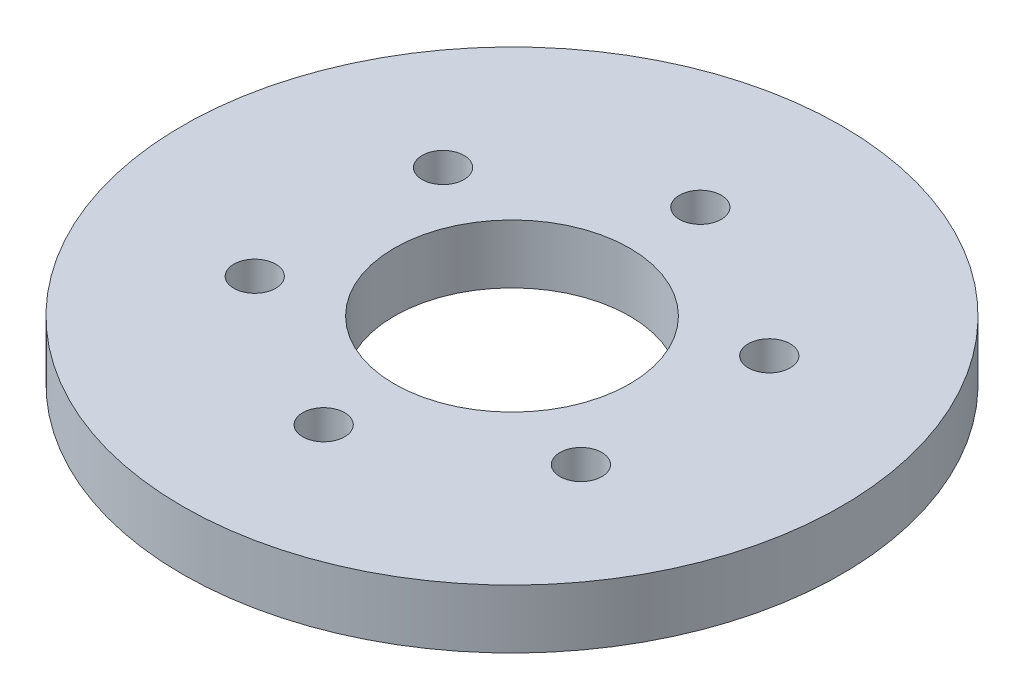
SolidWorks part; units mm, degrees
ref_plane "Front Plane" through (0, 0, 0) normal (0, 0, 1) x (1, 0, 0)
ref_plane "Top Plane" through (0, 0, 0) normal (0, 1, 0) x (1, 0, 0)
ref_plane "Right Plane" through (0, 0, 0) normal (1, 0, 0) x (0, 0, -1)
sketch "Sketch1" plane through (0, 0, 0) normal (0, 1, 0) x (1, 0, 0)
  line L0 (0, 10.16) -> (0, 0) construction
  circle A0 centre (0, 0) radius 6.35
  circle A1 centre (0, 0) radius 17.78
  point P4 (0, 10.16)
  point P6 (-8.7988, 5.08)
  point P7 (-29.4057, -6.7467)
  point P8 (0, 0)
  point P9 (-8.7988, -5.08)
  point P10 (0, -10.16)
  point P11 (8.7988, -5.08)
  point P12 (8.7988, 5.08)
  point P13 (0, 0)
  dimension "D1" = 12.7
  dimension "D2" = 35.56
  dimension "D3" = 10.16
  dimension "D4" = 6
extrude "Boss-Extrude1" add sketch "Sketch1" along normal blind 3.175
hole_wizard "Tap Drill for #4-40 Tap1" positions "Sketch2" profile "Sketch3" hole size "#4-40" standard "ANSI Inch" end condition through all
sketch "Sketch2" plane through (0, 0, 0) normal (0, -1, 0) x (-1, 0, 0)
  point P0 (0, -10.16)
  point P3 (-8.7988, -5.08)
  point P6 (-8.7988, 5.08)
  point P9 (0, 10.16)
  point P12 (8.7988, 5.08)
  point P15 (8.7988, -5.08)
sketch "Sketch3" plane through (0, 0, 10.16) normal (1, 0, 0) x (0, 0, -1)
  line L0 (0, 0) -> (0, 3.175)
  line L1 (0, 3.175) -> (1.1303, 3.175)
  line L2 (1.1303, 3.175) -> (1.1303, 0)
  line L5 (1.1303, 0) -> (0, 0)
  line L11 (0, -6.35) -> (0, 107.95) construction
  dimension "Thru Hole Dia." = 2.2606
  dimension "Thru Hole Depth" = 3.175
